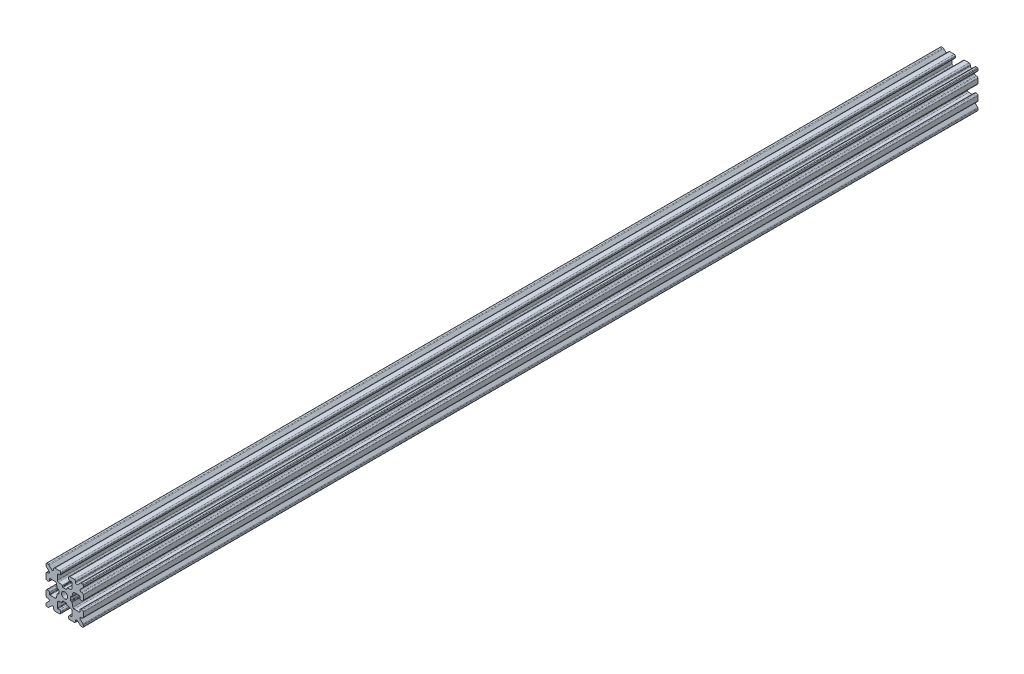
SolidWorks part; units mm, degrees
ref_plane "Front Plane" through (0, 0, 0) normal (0, 0, 1) x (1, 0, 0)
ref_plane "Top Plane" through (0, 0, 0) normal (0, 1, 0) x (1, 0, 0)
ref_plane "Right Plane" through (0, 0, 0) normal (1, 0, 0) x (0, 0, -1)
sketch "Sketch1" plane through (0, 0, 0) normal (0, 0, 1) x (1, 0, 0)
  line L1 (-7.5, -7.5) -> (7.5, -7.5)
  line L2 (-7.5, -7.5) -> (-7.5, 7.5)
  line L3 (-7.5, 7.5) -> (7.5, 7.5)
  line L4 (7.5, -7.5) -> (7.5, 7.5)
  line L5 (-7.5, -7.5) -> (7.5, 7.5) construction
  line L6 (-7.5, 7.5) -> (7.5, -7.5) construction
  circle A0 centre (0, 0) radius 1.25
  point P0 (0, 0)
  dimension "D2" = 2.5
  dimension "D1" = 15
extrude "Boss-Extrude1" add sketch "Sketch1" along normal mid plane 360
fillet "Fillet1" radius 0.25 4 edges at (7.5, -7.5, 0) (-7.5, -7.5, 0) (7.5, 7.5, 0) (-7.5, 7.5, 0)
sketch "Sketch2" plane through (0, 0, 180) normal (0, 0, 1) x (1, 0, 0)
  line L0 (-7.5, 7.25) -> (-7.5, -7.25) construction
  line L1 (-7.5, 1.6) -> (-6.1, 1.6)
  line L2 (-7.5, 1.6) -> (-7.5, -1.6)
  line L3 (-7.5, -1.6) -> (-6.1, -1.6)
  line L4 (-6.1, 1.6) -> (-6.1, 2.9)
  line L5 (0, 0) -> (-12.1036, 0) construction
  line L6 (-6.1, -2.9) -> (-3.4, -2.9)
  line L7 (0, 0) -> (-7.25, 7.25) construction
  line L8 (-6.1, 2.9) -> (-3.4, 2.9)
  line L9 (-3.4, -2.9) -> (-3.4, 2.9)
  line L10 (55, 0) -> (-55, 0) construction
  line L11 (-6.1, -2.9) -> (-6.1, -1.6)
  line L12 (2.9, 6.1) -> (1.6, 6.1)
  line L13 (2.9, 3.4) -> (-2.9, 3.4)
  line L14 (-2.9, 6.1) -> (-2.9, 3.4)
  line L15 (2.9, 6.1) -> (2.9, 3.4)
  line L16 (-1.6, 6.1) -> (-2.9, 6.1)
  line L17 (1.6, 7.5) -> (1.6, 6.1)
  line L18 (-1.6, 7.5) -> (1.6, 7.5)
  line L19 (-1.6, 7.5) -> (-1.6, 6.1)
  line L20 (-1.6, -7.5) -> (-1.6, -6.1)
  line L21 (-1.6, -7.5) -> (1.6, -7.5)
  line L22 (1.6, -7.5) -> (1.6, -6.1)
  line L23 (-1.6, -6.1) -> (-2.9, -6.1)
  line L24 (2.9, -6.1) -> (2.9, -3.4)
  line L25 (-2.9, -6.1) -> (-2.9, -3.4)
  line L26 (2.9, -3.4) -> (-2.9, -3.4)
  line L27 (2.9, -6.1) -> (1.6, -6.1)
  line L28 (6.1, -2.9) -> (6.1, -1.6)
  line L29 (3.4, -2.9) -> (3.4, 2.9)
  line L30 (6.1, 2.9) -> (3.4, 2.9)
  line L31 (6.1, -2.9) -> (3.4, -2.9)
  line L32 (6.1, 1.6) -> (6.1, 2.9)
  line L33 (7.5, -1.6) -> (6.1, -1.6)
  line L34 (7.5, 1.6) -> (7.5, -1.6)
  line L35 (7.5, 1.6) -> (6.1, 1.6)
  dimension "D1" = 3.2
  dimension "D2" = 5.8
  dimension "D3" = 1.4
  dimension "D4" = 2.7
extrude "Cut-Extrude1" cut sketch "Sketch2" against normal through all
sketch "Sketch4" plane through (0, 0, 180) normal (0, 0, 1) x (1, 0, 0)
  line L0 (-3.4, 2.9) -> (-2.75, 0)
  line L1 (55, 0) -> (-55, 0) construction
  line L2 (-2.75, 0) -> (-3.4, -2.9)
  line L3 (-3.4, -2.9) -> (-3.4, 2.9) construction
  line L4 (-3.4, 2.9) -> (-3.4, -2.9)
  line L5 (-2.9, 3.4) -> (0, 2.75)
  line L6 (0, 2.75) -> (2.9, 3.4)
  line L7 (2.9, 3.4) -> (-2.9, 3.4)
  line L8 (3.4, 2.9) -> (2.75, 0)
  line L9 (2.75, 0) -> (3.4, -2.9)
  line L10 (3.4, -2.9) -> (3.4, 2.9)
  line L11 (-2.9, -3.4) -> (0, -2.75)
  line L12 (0, -2.75) -> (2.9, -3.4)
  line L13 (2.9, -3.4) -> (-2.9, -3.4)
  circle A2 centre (0, 0) radius 2.75
  circle A3 centre (0, 0) radius 2.75 construction
  dimension "D1" = 1.5
extrude "Cut-Extrude3" cut sketch "Sketch4" against normal through all
fillet "Fillet3" radius 0.5 16 edges at (-6.1, -1.6, 0) (-7.5, -1.6, 0) (-6.1, 1.6, 0) (-7.5, 1.6, 0) (-1.6, -7.5, 0) (-1.6, -6.1, 0) (1.6, -7.5, 0) (1.6, -6.1, 0) (6.1, -1.6, 0) (7.5, -1.6, 0) (7.5, 1.6, 0) (6.1, 1.6, 0) (1.6, 7.5, 0) (1.6, 6.1, 0) (-1.6, 7.5, 0) (-1.6, 6.1, 0)
fillet "Fillet4" radius 0.5 8 edges at (-3.4, 2.9, 0) (-3.4, -2.9, 0) (2.9, -3.4, 0) (-2.9, -3.4, 0) (3.4, -2.9, 0) (3.4, 2.9, 0) (-2.9, 3.4, 0) (2.9, 3.4, 0)
fillet "Fillet5" radius 3 4 edges at (0, -2.75, 0) (2.75, 0, 0) (-2.75, 0, 0) (0, 2.75, 0)
fillet "Fillet6" radius 0.2 8 edges at (-2.9, -6.1, 0) (2.9, -6.1, 0) (6.1, -2.9, 0) (6.1, 2.9, 0) (2.9, 6.1, 0) (-2.9, 6.1, 0) (-6.1, -2.9, 0) (-6.1, 2.9, 0)
sketch "Sketch5" plane through (0, 0, 180) normal (0, 0, 1) x (1, 0, 0)
  line L0 (0, 0) -> (-7.25, 7.25) construction
  line L1 (-7.5, 6.4393) -> (-5.4607, 4.4)
  line L2 (-6.4393, 7.5) -> (-4.4, 5.4607)
  line L3 (-7.5, 4.4) -> (-5.4607, 4.4)
  line L4 (-3.8003, 2.9) -> (-5.9, 2.9) construction
  line L5 (0, 0) -> (-12.1819, 0) construction
  line L6 (-4.4, 7.5) -> (-4.4, 5.4607)
  line L7 (-2.9, 5.9) -> (-2.9, 3.8003) construction
  line L8 (-7.5, 6.4393) -> (-7.5, 4.4)
  line L9 (-7.5, 7.25) -> (-7.5, 2.1) construction
  line L10 (2.1, -7.5) -> (7.25, -7.5) construction
  line L11 (7.5, -7.25) -> (7.5, -2.1) construction
  line L12 (7.25, 7.5) -> (2.1, 7.5) construction
  line L13 (-2.1, 7.5) -> (-7.25, 7.5) construction
  line L14 (-4.4, 7.5) -> (-6.4393, 7.5)
  line L16 (55, 0) -> (-55, 0) construction
  line L17 (0, 0) -> (0, 10.993) construction
  line L18 (0, -54.6431) -> (0, 54.6431) construction
  line L20 (4.4, 7.5) -> (6.4393, 7.5)
  line L22 (7.5, 6.4393) -> (7.5, 4.4)
  line L23 (4.4, 7.5) -> (4.4, 5.4607)
  line L24 (7.5, 4.4) -> (5.4607, 4.4)
  line L25 (6.4393, 7.5) -> (4.4, 5.4607)
  line L26 (7.5, 6.4393) -> (5.4607, 4.4)
  line L27 (7.5, -6.4393) -> (5.4607, -4.4)
  line L28 (6.4393, -7.5) -> (4.4, -5.4607)
  line L29 (7.5, -4.4) -> (5.4607, -4.4)
  line L30 (4.4, -7.5) -> (4.4, -5.4607)
  line L31 (7.5, -6.4393) -> (7.5, -4.4)
  line L33 (4.4, -7.5) -> (6.4393, -7.5)
  line L36 (-4.4, -7.5) -> (-6.4393, -7.5)
  line L38 (-7.5, -6.4393) -> (-7.5, -4.4)
  line L39 (-4.4, -7.5) -> (-4.4, -5.4607)
  line L40 (-7.5, -4.4) -> (-5.4607, -4.4)
  line L41 (-6.4393, -7.5) -> (-4.4, -5.4607)
  line L42 (-7.5, -6.4393) -> (-5.4607, -4.4)
  dimension "D1" = 1.5
  dimension "D2" = 1.5
  dimension "D3" = 1.5
extrude "Cut-Extrude4" cut sketch "Sketch5" against normal through all
fillet "Fillet8" radius 0.5 24 edges at (-5.4607, 4.4, 0) (-7.5, 4.4, 0) (-5.4607, -4.4, 0) (-7.5, -4.4, 0) (-4.4, -7.5, 0) (-4.4, -5.4607, 0) (4.4, -7.5, 0) (4.4, -5.4607, 0) (5.4607, -4.4, 0) (7.5, -4.4, 0) (7.5, 4.4, 0) (5.4607, 4.4, 0) (4.4, 5.4607, 0) (4.4, 7.5, 0) (-4.4, 5.4607, 0) (-4.4, 7.5, 0) (-6.4393, 7.5, 0) (-7.5, 6.4393, 0) (6.4393, 7.5, 0) (7.5, 6.4393, 0) (6.4393, -7.5, 0) (7.5, -6.4393, 0) (-6.4393, -7.5, 0) (-7.5, -6.4393, 0)
sketch "Sketch6" plane through (0, 0, 180) normal (0, 0, 1) x (1, 0, 0)
  line L0 (0, 0) -> (0, 11.013) construction
  line L1 (0.6561, 2.8971) -> (2.1235, 2.8971) construction
  line L2 (0, -54.6431) -> (0, 54.6431) construction
  line L3 (0, 0) -> (7.25, 7.25) construction
  line L4 (7.5, 0.8255) -> (7.5, -0.8255)
  line L5 (2.3471, 0.8255) -> (7.5, 0.8255)
  line L6 (0, 0) -> (12.4016, 0) construction
  line L7 (0.8255, -7.5) -> (-0.8255, -7.5)
  line L8 (2.3471, -0.8255) -> (2.3471, 0.8255)
  line L9 (0.8255, -2.3471) -> (0.8255, -7.5)
  line L10 (7.5, -0.8255) -> (2.3471, -0.8255)
  line L11 (-7.5, -0.8255) -> (-2.3471, -0.8255)
  line L12 (-2.3471, -0.8255) -> (-2.3471, 0.8255)
  line L13 (-0.8255, -2.3471) -> (0.8255, -2.3471)
  line L14 (-0.8255, 7.5) -> (-0.8255, 2.3471)
  line L15 (-0.8255, 2.3471) -> (0.8255, 2.3471)
  line L16 (-0.8255, -7.5) -> (-0.8255, -2.3471)
  line L17 (0.8255, 2.3471) -> (0.8255, 7.5)
  line L18 (0.8255, 7.5) -> (-0.8255, 7.5)
  line L19 (3.9, 7.5) -> (2.1, 7.5) construction
  line L20 (-2.3471, 0.8255) -> (-7.5, 0.8255)
  line L21 (-7.5, 0.8255) -> (-7.5, -0.8255)
  point P5 (0, -2.5973)
  point P7 (0, 2.5973)
  dimension "D3" = 0.55
  dimension "D1" = 1.651
extrude "Cut-Extrude5" cut sketch "Sketch6" against normal through all
fillet "Fillet10" radius 0.2 16 edges at (-2.935, 0.8255, 0) (-2.935, -0.8255, 0) (2.935, -0.8255, 0) (2.935, 0.8255, 0) (0.8255, 2.935, 0) (-0.8255, 2.935, 0) (-2.3471, 0.8255, 0) (-2.3471, -0.8255, 0) (0.8255, 2.3471, 0) (-0.8255, 2.3471, 0) (2.3471, 0.8255, 0) (2.3471, -0.8255, 0) (0.8255, -2.935, 0) (0.8255, -2.3471, 0) (-0.8255, -2.3471, 0) (-0.8255, -2.935, 0)
